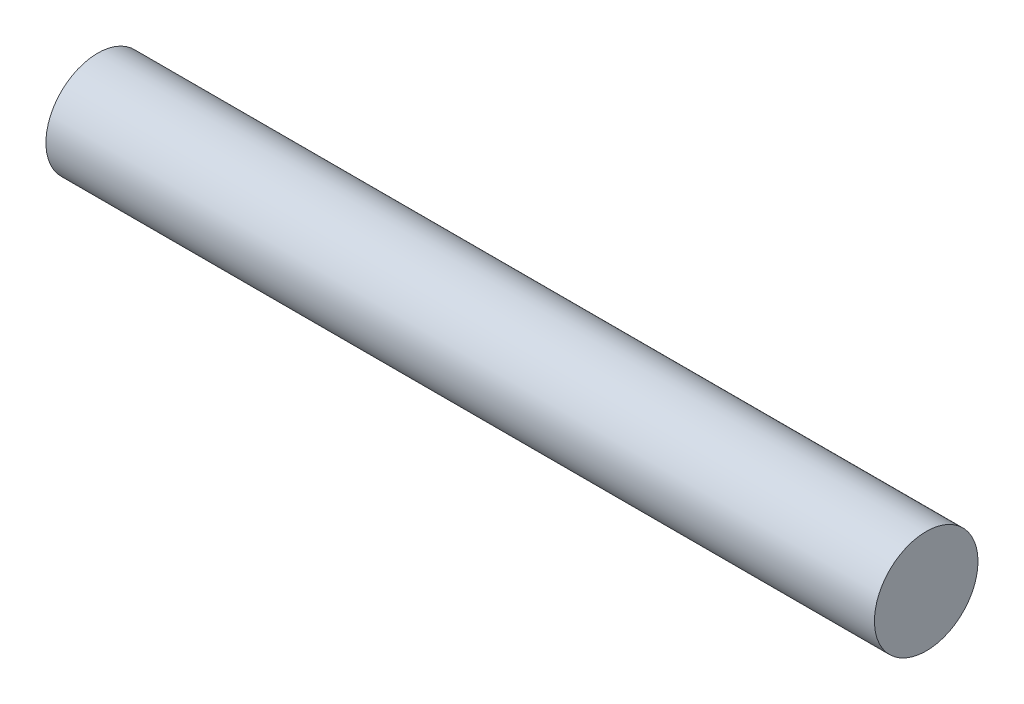
SolidWorks part; units mm, degrees
ref_plane "Front Plane" through (0, 0, 0) normal (0, 0, 1) x (1, 0, 0)
ref_plane "Top Plane" through (0, 0, 0) normal (0, 1, 0) x (1, 0, 0)
ref_plane "Right Plane" through (0, 0, 0) normal (1, 0, 0) x (0, 0, -1)
sketch "Sketch1" plane through (0, 0, 0) normal (1, 0, 0) x (0, -1, 0)
  circle A0 centre (0, 0) radius 25
  dimension "D1" = 50
extrude "Boss-Extrude1" add sketch "Sketch1" along normal mid plane 400
